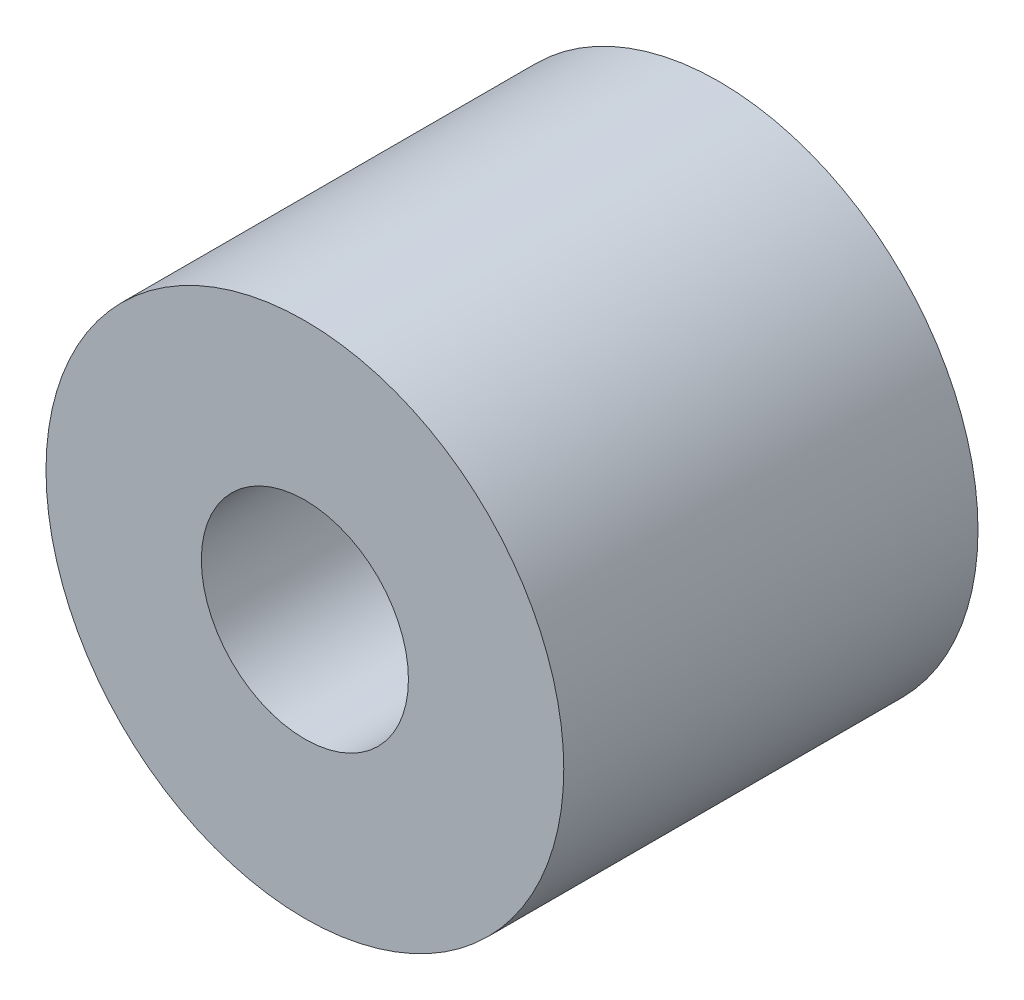
SolidWorks part; units mm, degrees
ref_plane "Front Plane" through (0, 0, 0) normal (0, 0, 1) x (1, 0, 0)
ref_plane "Top Plane" through (0, 0, 0) normal (0, 1, 0) x (1, 0, 0)
ref_plane "Right Plane" through (0, 0, 0) normal (1, 0, 0) x (0, 0, -1)
sketch "Sketch1" plane through (0, 0, 0) normal (0, 0, 1) x (1, 0, 0)
  circle A0 centre (0, 0) radius 7.9375
  circle A1 centre (0, 0) radius 3.175
  dimension "D1" = 15.875
  dimension "D2" = 6.35
extrude "Boss-Extrude1" add sketch "Sketch1" along normal blind 12.7
